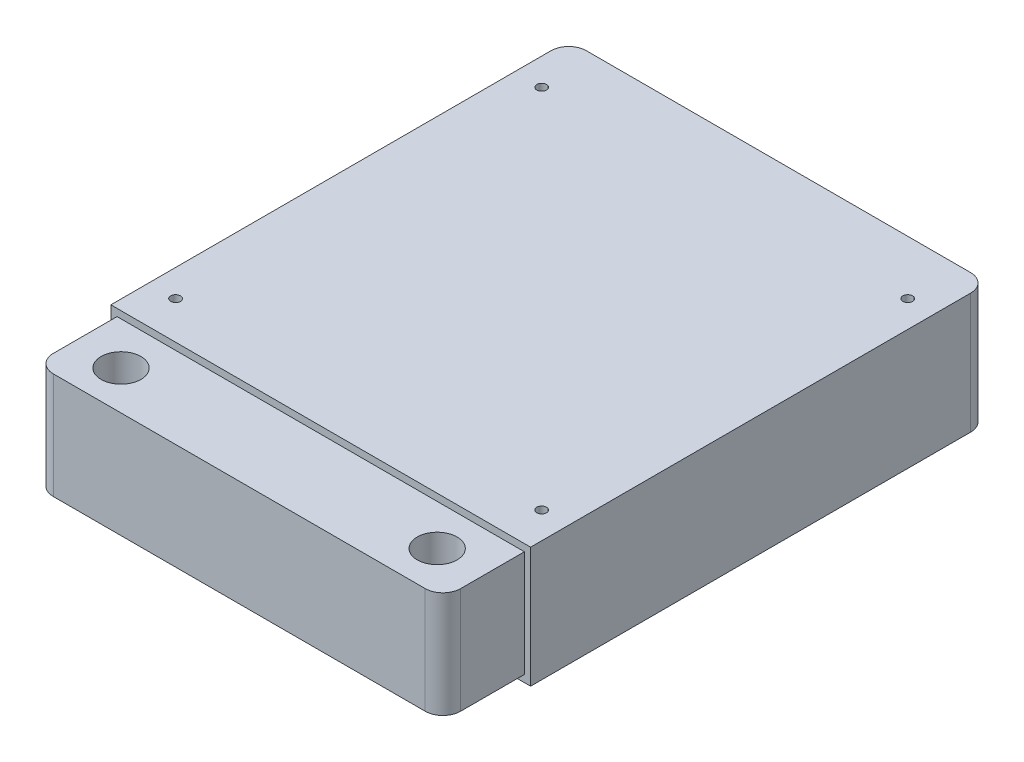
SolidWorks part; units mm, degrees
ref_plane "Front Plane" through (0, 0, 0) normal (0, 0, 1) x (1, 0, 0)
ref_plane "Top Plane" through (0, 0, 0) normal (0, 1, 0) x (1, 0, 0)
ref_plane "Right Plane" through (0, 0, 0) normal (1, 0, 0) x (0, 0, -1)
sketch "Sketch1" plane through (0, 0, 0) normal (0, 1, 0) x (1, 0, 0)
  line L2 (-143.4336, 119.2248) -> (-23.0376, 119.2248)
  line L3 (-143.4336, 119.2248) -> (-143.4336, -12.0932)
  line L4 (-143.4336, -12.0932) -> (-23.0376, -12.0932)
  line L5 (-23.0376, 119.2248) -> (-23.0376, -12.0932)
  line L6 (-143.4336, 119.2248) -> (-23.0376, -12.0932) construction
  line L7 (-143.4336, -12.0932) -> (-23.0376, 119.2248) construction
  point P2 (-83.2356, 53.5658)
  dimension "D1" = 120.396
  dimension "D2" = 131.318
extrude "Boss-Extrude1" add sketch "Sketch1" along normal blind 34.544
sketch "Sketch2" plane through (0, 34.544, 0) normal (0, 1, 0) x (1, 0, 0)
  line L0 (-143.4336, 103.7308) -> (-23.0376, 103.7308) construction
  line L1 (-143.4336, 119.2248) -> (-143.4336, -12.0932) construction
  line L2 (-23.0376, -12.0932) -> (-23.0376, 119.2248) construction
  line L3 (-143.4336, -1.2692) -> (-23.0376, -1.2692) construction
  line L4 (-135.6866, 119.2248) -> (-135.6866, -12.0932) construction
  line L5 (-23.0376, 119.2248) -> (-143.4336, 119.2248) construction
  line L6 (-143.4336, -12.0932) -> (-23.0376, -12.0932) construction
  line L7 (-30.6866, 119.2248) -> (-30.6866, -12.0932) construction
  circle A0 centre (-135.6866, 103.7308) radius 1.397
  circle A1 centre (-30.6866, 103.7308) radius 1.397
  circle A2 centre (-135.6866, -1.2692) radius 1.397
  circle A3 centre (-30.6866, -1.2692) radius 1.397
  dimension "D5" = 105
  dimension "D1" = 15.494
  dimension "D2" = 105
  dimension "D3" = 105
  dimension "D4" = 7.747
extrude "Cut-Extrude1" cut sketch "Sketch2" against normal through all
sketch "Sketch3" plane through (0, 0, 12.0932) normal (0, 0, 1) x (1, 0, 0)
  line L0 (-143.4336, 17.272) -> (-23.0376, 17.272) construction
  line L1 (-143.4336, 34.544) -> (-143.4336, 0) construction
  line L2 (-23.0376, 34.544) -> (-23.0376, 0) construction
  line L3 (-83.2356, 34.544) -> (-83.2356, 0) construction
  line L4 (-143.4336, 34.544) -> (-23.0376, 34.544) construction
  line L5 (-143.4336, 0) -> (-23.0376, 0) construction
  line L7 (-141.6556, 2.032) -> (-24.8156, 2.032)
  line L8 (-141.6556, 2.032) -> (-141.6556, 32.512)
  line L9 (-141.6556, 32.512) -> (-24.8156, 32.512)
  line L10 (-24.8156, 2.032) -> (-24.8156, 32.512)
  line L11 (-141.6556, 2.032) -> (-24.8156, 32.512) construction
  line L12 (-141.6556, 32.512) -> (-24.8156, 2.032) construction
  point P12 (-83.2356, 17.272)
  dimension "D1" = 116.84
  dimension "D2" = 30.48
extrude "Boss-Extrude2" add sketch "Sketch3" along normal blind 23.368
sketch "Sketch4" plane through (0, 32.512, 0) normal (0, 1, 0) x (1, 0, 0)
  line L0 (-128.3206, -35.4612) -> (-128.3206, -12.0932) construction
  line L1 (-24.8156, -35.4612) -> (-141.6556, -35.4612) construction
  line L2 (-24.8156, -12.0932) -> (-141.6556, -12.0932) construction
  line L3 (-38.1506, -35.4612) -> (-38.1506, -12.0932) construction
  line L4 (-141.6556, -23.6502) -> (-24.8156, -23.6502) construction
  line L5 (-141.6556, -35.4612) -> (-141.6556, -12.0932) construction
  line L6 (-24.8156, -35.4612) -> (-24.8156, -12.0932) construction
  circle A0 centre (-128.3206, -24.2882) radius 5.715
  circle A1 centre (-38.1506, -23.7772) radius 5.715
  dimension "D1" = 13.335
  dimension "D2" = 11.811
  dimension "D3" = 13.335
extrude "Cut-Extrude2" cut sketch "Sketch4" against normal through all
fillet "Fillet1" radius 5.08 4 edges at (-23.0376, 17.272, -119.2248) (-143.4336, 17.272, -119.2248) (-141.6556, 17.272, 35.4612) (-24.8156, 17.272, 35.4612)
